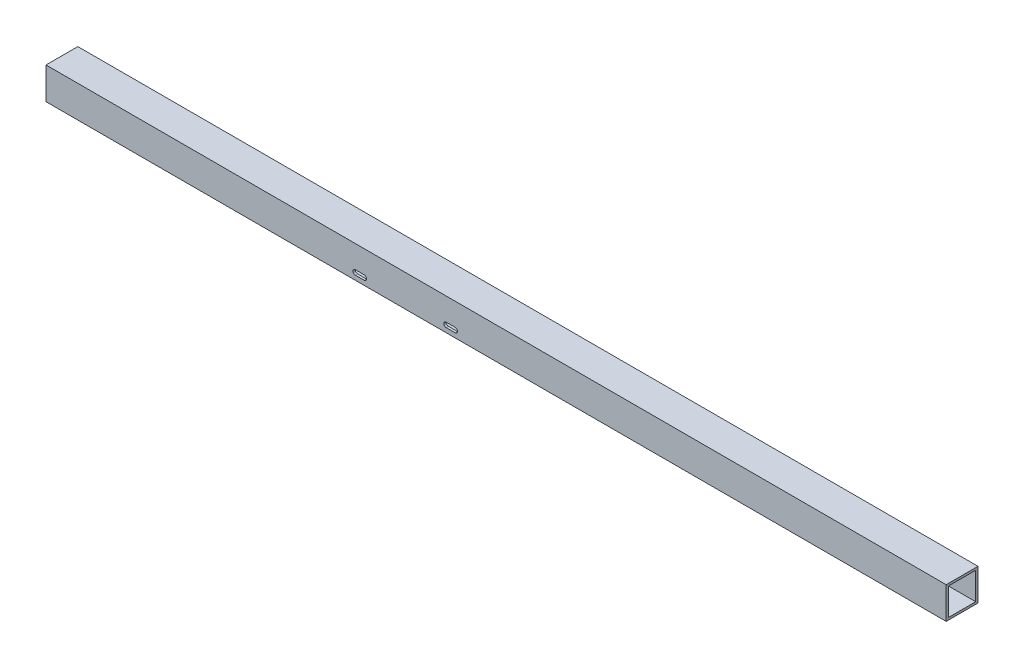
SolidWorks part; units mm, degrees
material "6061 Alloy"
ref_plane "Front Plane" through (0, 0, 0) normal (0, 0, 1) x (1, 0, 0)
ref_plane "Top Plane" through (0, 0, 0) normal (0, 1, 0) x (1, 0, 0)
ref_plane "Right Plane" through (0, 0, 0) normal (1, 0, 0) x (0, 0, -1)
sketch "Sketch1" plane through (0, 0, 0) normal (1, 0, 0) x (0, 0, -1)
  line L0 (41.275, 41.275) -> (3.175, 41.275)
  line L1 (0, 0) -> (44.45, 0)
  line L2 (44.45, 0) -> (44.45, 44.45)
  line L3 (44.45, 44.45) -> (0, 44.45)
  line L4 (0, 44.45) -> (0, 0)
  line L5 (3.175, 41.275) -> (3.175, 3.175)
  line L6 (3.175, 3.175) -> (41.275, 3.175)
  line L7 (41.275, 3.175) -> (41.275, 41.275)
  circle A0 centre (22.225, 22.225) radius 22.225 construction
  dimension "D1" = 44.45
  dimension "D2" = 3.175
extrude "Boss-Extrude1" add sketch "Sketch1" along normal mid plane 1257.3
sketch "Sketch2" plane through (0, 0, 0) normal (0, 0, 1) x (1, 0, 0)
  line L0 (-196.723, 9.525) -> (-184.277, 9.525) construction
  line L1 (-196.723, 12.827) -> (-184.277, 12.827)
  line L2 (-196.723, 6.223) -> (-184.277, 6.223)
  line L3 (-69.723, 9.525) -> (-57.277, 9.525) construction
  line L4 (-69.723, 12.827) -> (-57.277, 12.827)
  line L5 (-69.723, 6.223) -> (-57.277, 6.223)
  line L6 (628.65, 44.45) -> (-628.65, 44.45) construction
  line L7 (628.65, 0) -> (-628.65, 0) construction
  arc A0 (-196.723, 12.827) -> (-196.723, 6.223) centre (-196.723, 9.525) ccw
  arc A1 (-184.277, 6.223) -> (-184.277, 12.827) centre (-184.277, 9.525) ccw
  arc A2 (-69.723, 12.827) -> (-69.723, 6.223) centre (-69.723, 9.525) ccw
  arc A3 (-57.277, 6.223) -> (-57.277, 12.827) centre (-57.277, 9.525) ccw
  point P2 (-190.5, 9.525)
  point P7 (-63.5, 9.525)
  point P16 (0, 44.45)
  dimension "D1" = 63.5
  dimension "D2" = 127
  dimension "D3" = 12.446
  dimension "D4" = 6.604
  dimension "D5" = 9.525
extrude "Cut-Extrude1" cut sketch "Sketch2" against normal up to next
